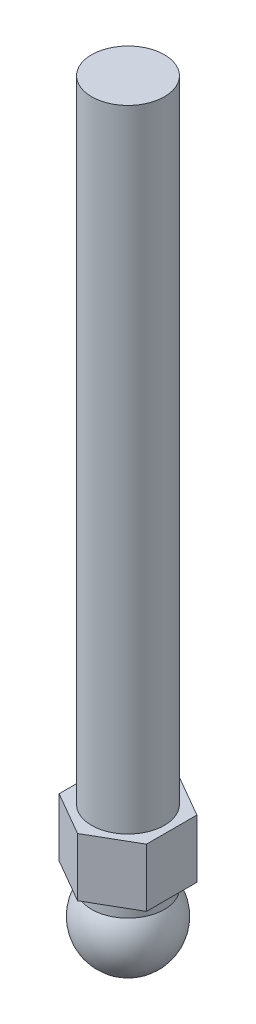
SolidWorks part; units mm, degrees
ref_plane "Front Plane" through (0, 0, 0) normal (0, 0, 1) x (1, 0, 0)
ref_plane "Top Plane" through (0, 0, 0) normal (0, 1, 0) x (1, 0, 0)
ref_plane "Right Plane" through (0, 0, 0) normal (1, 0, 0) x (0, 0, -1)
sketch "Sketch1" plane through (0, 0, 0) normal (0, 0, 1) x (1, 0, 0)
  line L0 (0, 109.4946) -> (0, -18.8597) construction
  line L1 (-5, 3.3166) -> (-5, 100)
  line L2 (-5, 100) -> (0, 100)
  line L3 (0, -6) -> (0, 100)
  arc A0 (-5, 3.3166) -> (0, -6) centre (0, 0) ccw
  dimension "D1" = 12
  dimension "D2" = 100
  dimension "D3" = 10
revolve "Revolve1" add sketch "Sketch1" angle 360 about L0
ref_plane "Plane1" through (0, 3.3166, 0) normal (0, 1, 0) x (1, 0, 0)
ref_plane "Plane2" through (0, 5.3166, 0) normal (0, 1, 0) x (1, 0, 0)
sketch "Sketch4" plane through (0, 5.3166, 0) normal (0, 1, 0) x (1, 0, 0)
  line L1 (0, 6.9282) -> (-6, 3.4641)
  line L2 (-6, 3.4641) -> (-6, -3.4641)
  line L3 (-6, -3.4641) -> (0, -6.9282)
  line L4 (0, -6.9282) -> (6, -3.4641)
  line L5 (6, -3.4641) -> (6, 3.4641)
  line L6 (6, 3.4641) -> (0, 6.9282)
  circle A0 centre (0, 0) radius 6 construction
  dimension "D1" = 12
extrude "Boss-Extrude3" add sketch "Sketch4" along normal blind 8
